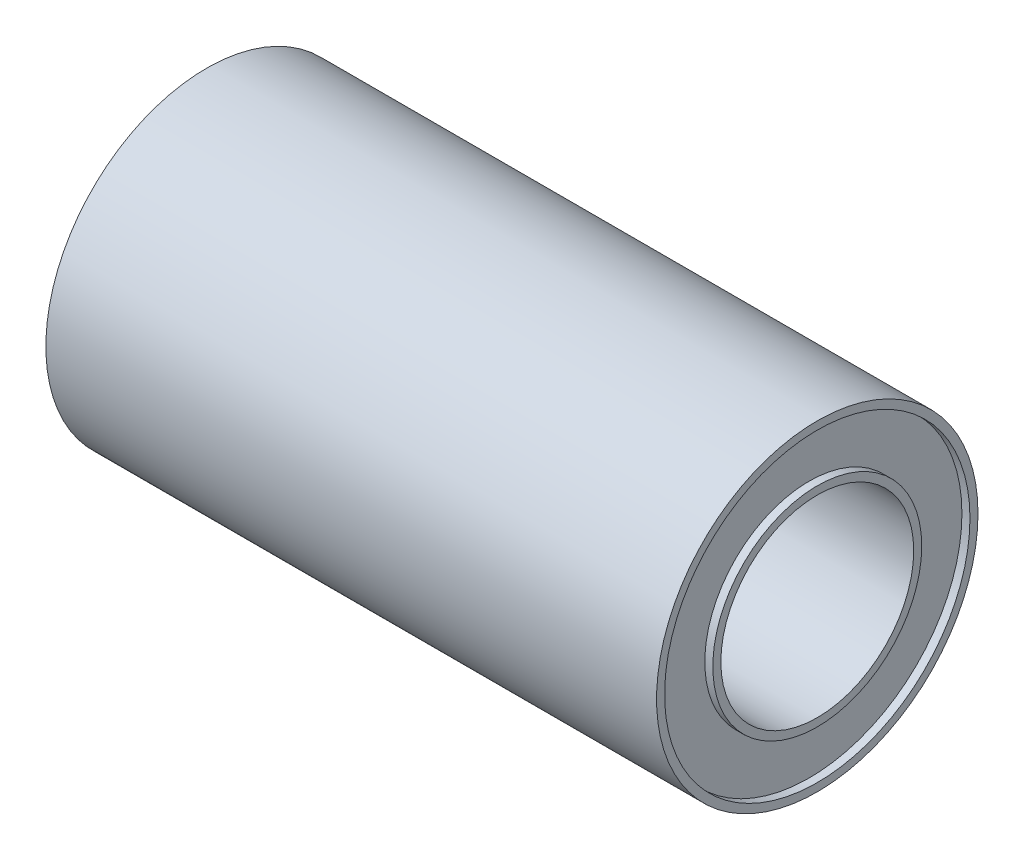
SolidWorks part; units mm, degrees
ref_plane "Front Plane" through (0, 0, 0) normal (0, 0, 1) x (1, 0, 0)
ref_plane "Top Plane" through (0, 0, 0) normal (0, 1, 0) x (1, 0, 0)
ref_plane "Right Plane" through (0, 0, 0) normal (1, 0, 0) x (0, 0, -1)
sketch "Sketch1" plane through (0, 0, 0) normal (1, 0, 0) x (0, 0, -1)
  circle A0 centre (0, 0) radius 5
  circle A1 centre (0, 0) radius 3
  dimension "D1" = 6
  dimension "D2" = 10
extrude "Extrude1" add sketch "Sketch1" along normal blind 19
sketch "Sketch2" plane through (19, 0, 0) normal (1, 0, 0) x (0, 0, -1)
  circle A2 centre (0, 0) radius 4.75
  circle A3 centre (0, 0) radius 4.75
  circle A5 centre (0, 0) radius 3.25
  circle A6 centre (0, 0) radius 3.25
  dimension "D1" = 0.25
  dimension "D2" = 0.25
extrude "Cut-Extrude1" cut sketch "Sketch2" against normal blind 0.25
ref_plane "Plane1" through (9.5, 0, 0) normal (-1, 0, 0) x (0, 0, 1)
mirror "Mirror1" about plane through (9.5, 0, 0) normal (-1, 0, 0) of "Cut-Extrude1"
